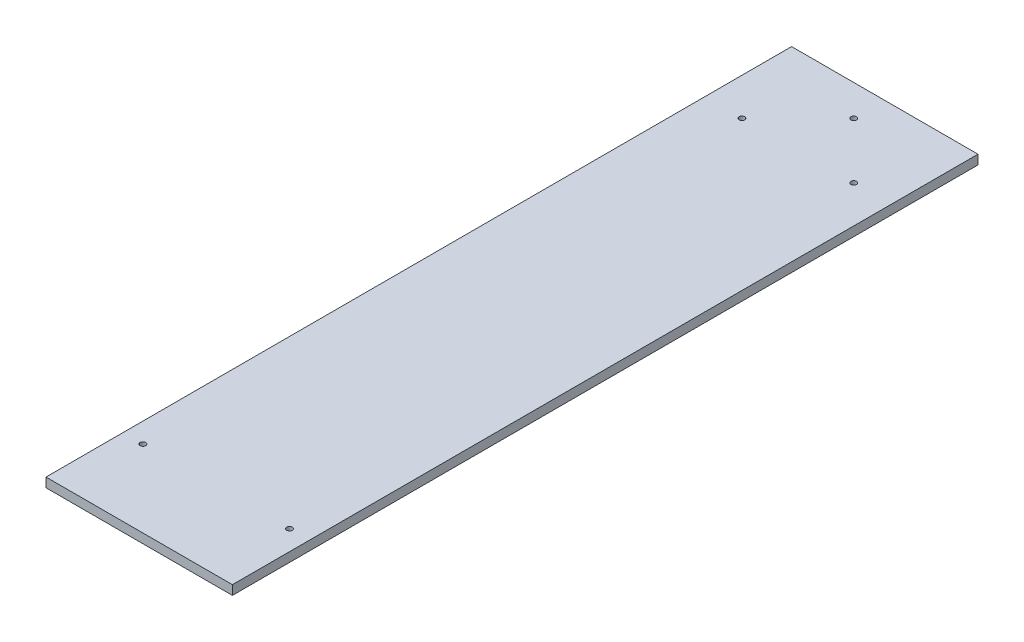
SolidWorks part; units mm, degrees
ref_plane "Front Plane" through (0, 0, 0) normal (0, 0, 1) x (1, 0, 0)
ref_plane "Top Plane" through (0, 0, 0) normal (0, 1, 0) x (1, 0, 0)
ref_plane "Right Plane" through (0, 0, 0) normal (1, 0, 0) x (0, 0, -1)
sketch "Sketch1" plane through (0, 0, 0) normal (0, 1, 0) x (1, 0, 0)
  line L1 (-150, 600) -> (150, 600)
  line L2 (-150, 600) -> (-150, -600)
  line L3 (-150, -600) -> (150, -600)
  line L4 (150, 600) -> (150, -600)
  line L5 (-150, 600) -> (150, -600) construction
  line L6 (-150, -600) -> (150, 600) construction
  point P0 (0, 0)
  dimension "D1" = 1200
  dimension "D2" = 300
extrude "Boss-Extrude1" add sketch "Sketch1" along normal blind 15
sketch "Sketch3" plane through (0, 15, 0) normal (0, 1, 0) x (1, 0, 0)
  line L0 (0, 0) -> (0, 753.4693) construction
  line L1 (150, 600) -> (-150, 600) construction
  circle A0 centre (-90, 460) radius 4.5
  circle A1 centre (90, 460) radius 4.5
  circle A2 centre (0, 550) radius 4.5
  circle A3 centre (-118, -476) radius 4.5
  circle A4 centre (118, -476) radius 4.5
  dimension "D1" = 9
  dimension "D2" = 180
  dimension "D3" = 90
  dimension "D4" = 50
  dimension "D5" = 936
  dimension "D6" = 236
extrude "Cut-Extrude1" cut sketch "Sketch3" against normal through all
